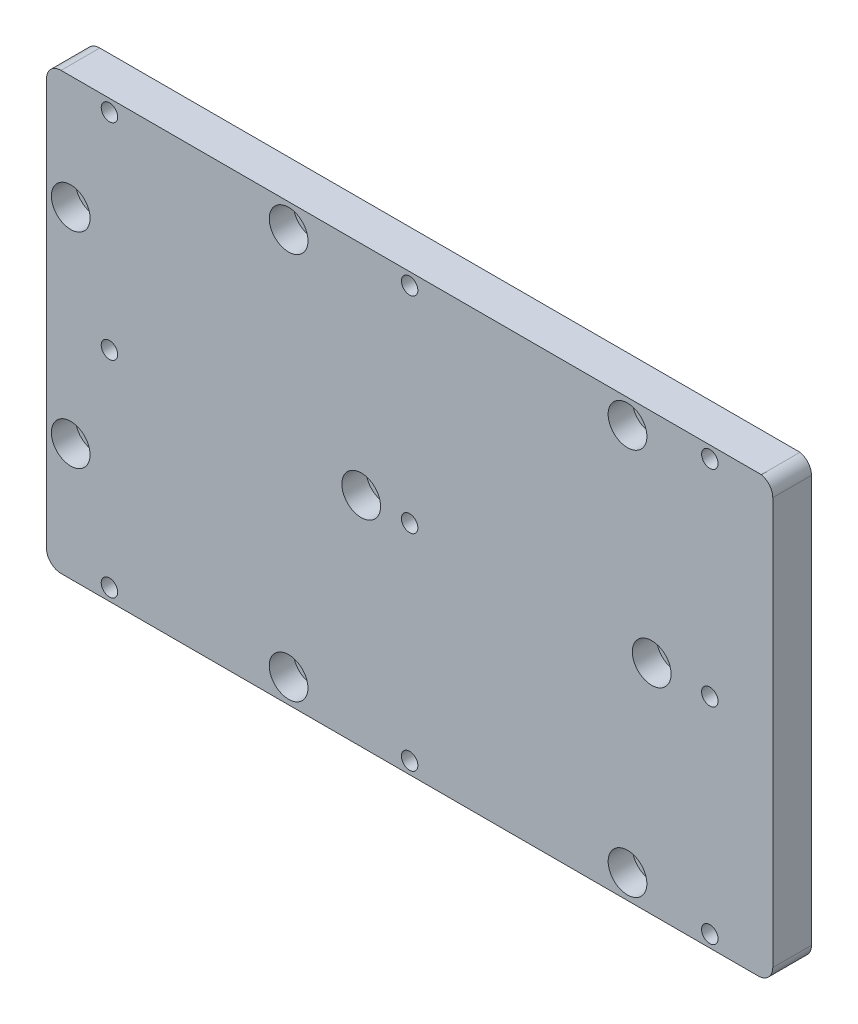
SolidWorks part; units mm, degrees
ref_plane "Plan de face" through (0, 0, 0) normal (0, 0, 1) x (1, 0, 0)
ref_plane "Plan de dessus" through (0, 0, 0) normal (0, 1, 0) x (1, 0, 0)
ref_plane "Plan de droite" through (0, 0, 0) normal (1, 0, 0) x (0, 0, -1)
sketch "Esquisse1" plane through (0, 0, 0) normal (0, 0, 1) x (1, 0, 0)
  line L5 (2.9684, 10.0302) -> (146.9684, 10.0302)
  line L6 (-0.0316, 13.0302) -> (-0.0316, 97.0302)
  line L7 (149.9684, 13.0302) -> (149.9684, 97.0969)
  line L10 (2.9684, 100.0302) -> (147.5976, 100.0302)
  arc A0 (2.9684, 10.0302) -> (-0.0316, 13.0302) centre (2.9684, 13.0302) cw
  arc A1 (146.9684, 10.0302) -> (149.9684, 13.0302) centre (146.9684, 13.0302) ccw
  arc A2 (147.5976, 100.0302) -> (149.9684, 97.0969) centre (146.9684, 97.0969) cw
  arc A3 (-0.0316, 97.0302) -> (2.9684, 100.0302) centre (2.9684, 97.0302) cw
  circle A4 centre (12.9684, 97.5302) radius 1.25
  circle A5 centre (74.9684, 97.5302) radius 1.25
  circle A6 centre (136.9684, 97.5302) radius 1.25
  circle A7 centre (12.9684, 55.0302) radius 1.25
  circle A8 centre (74.9684, 55.0302) radius 1.25
  circle A9 centre (136.9684, 55.0302) radius 1.25
  circle A10 centre (136.9684, 12.5302) radius 1.25
  circle A11 centre (74.9684, 12.5302) radius 1.25
  circle A12 centre (12.9684, 12.5302) radius 1.25
  point P17 (-0.0316, 100.0302)
  dimension "D1" = 3
  dimension "D14" = 85
  dimension "D2" = 13
  dimension "D3" = 13
  dimension "D4" = 75
  dimension "D5" = 13
  dimension "D6" = 75
  dimension "D7" = 13
  dimension "D8" = 2.5
  dimension "D9" = 2.5
  dimension "D10" = 2.5
  dimension "D11" = 13
  dimension "D12" = 75
  dimension "D13" = 13
  dimension "D15" = 2.5
  dimension "D16" = 2.5
  dimension "D17" = 2.5
  dimension "D18" = 150
  dimension "D19" = 90
  dimension "D20" = 75
  dimension "D21" = 45
  dimension "D22" = 45
  dimension "D23" = 45
extrude "Boss.-Extru.1" add sketch "Esquisse1" along normal blind 8
hole_wizard "Trou taraudé M3" positions "Esquisse9" profile "Esquisse10" hole size "M3" standard "ISO" end condition through all
sketch "Esquisse9" plane through (0, 0, 8) normal (0, 0, 1) x (1, 0, 0)
  point P0 (12.9684, 97.5302)
  point P3 (12.9684, 55.0302)
  point P6 (12.9684, 12.5302)
  point P9 (74.9684, 12.5302)
  point P12 (74.9684, 55.0302)
  point P15 (74.9684, 97.5302)
  point P18 (136.9684, 97.5302)
  point P21 (136.9684, 55.0302)
  point P24 (136.9684, 12.5302)
sketch "Esquisse10" plane through (12.9684, 97.5302, 8) normal (1, 0, 0) x (0, -1, 0)
  line L0 (0, 0) -> (0, 8)
  line L1 (0, 8) -> (1.7, 8)
  line L2 (1.7, 8) -> (1.7, 0)
  line L5 (1.7, 0) -> (0, 0)
  line L11 (0, -6.35) -> (0, 107.95) construction
  dimension "Diamètre du perçage jusqu'au prochain" = 3.4
  dimension "Profondeur du perçage jusqu'au prochain" = 8
sketch "Esquisse4" plane through (0, 0, 8) normal (0, 0, 1) x (1, 0, 0)
  line L0 (2.9684, 10.0302) -> (146.9684, 10.0302) construction
  line L1 (-0.0316, 97.0302) -> (-0.0316, 13.0302) construction
  line L2 (147.5976, 100.0302) -> (2.9684, 100.0302) construction
  line L3 (149.9684, 13.0302) -> (149.9684, 97.0969) construction
  circle A0 centre (119.9684, 95.0302) radius 1.6
  circle A1 centre (49.9684, 95.0302) radius 1.6
  circle A2 centre (4.9684, 76.5561) radius 1.6
  circle A3 centre (4.9684, 34.2503) radius 1.6
  circle A4 centre (49.9684, 15.0302) radius 1.6
  circle A5 centre (119.9684, 15.0302) radius 1.6
  circle A6 centre (64.9684, 55.0302) radius 1.6
  circle A7 centre (124.9684, 55.0302) radius 1.6
  point P24 (0, 0)
  dimension "D1" = 5
  dimension "D13" = 45
  dimension "D2" = 5
  dimension "D3" = 5
  dimension "D4" = 5
  dimension "D5" = 5
  dimension "D6" = 5
  dimension "D7" = 30
  dimension "D8" = 30
  dimension "D9" = 70
  dimension "D10" = 70
  dimension "D11" = 45
  dimension "D12" = 45
  dimension "D14" = 45
  dimension "D15" = 25
  dimension "D16" = 60
  dimension "D17" = 23.4741
  dimension "D18" = 24.2201
extrude "Enlèv. mat.-Extru.1" cut sketch "Esquisse4" against normal through all
sketch "Esquisse5" plane through (0, 0, 8) normal (0, 0, 1) x (1, 0, 0)
  circle A0 centre (49.9684, 95.0302) radius 4
  circle A1 centre (119.9684, 95.0302) radius 4
  circle A2 centre (124.9684, 55.0302) radius 4
  circle A3 centre (64.9684, 55.0302) radius 4
  circle A4 centre (4.9684, 76.5561) radius 4
  circle A5 centre (4.9684, 34.2503) radius 4
  circle A6 centre (49.9684, 15.0302) radius 4
  circle A7 centre (119.9684, 15.0302) radius 4
extrude "Enlèv. mat.-Extru.2" cut sketch "Esquisse5" against normal blind 5
